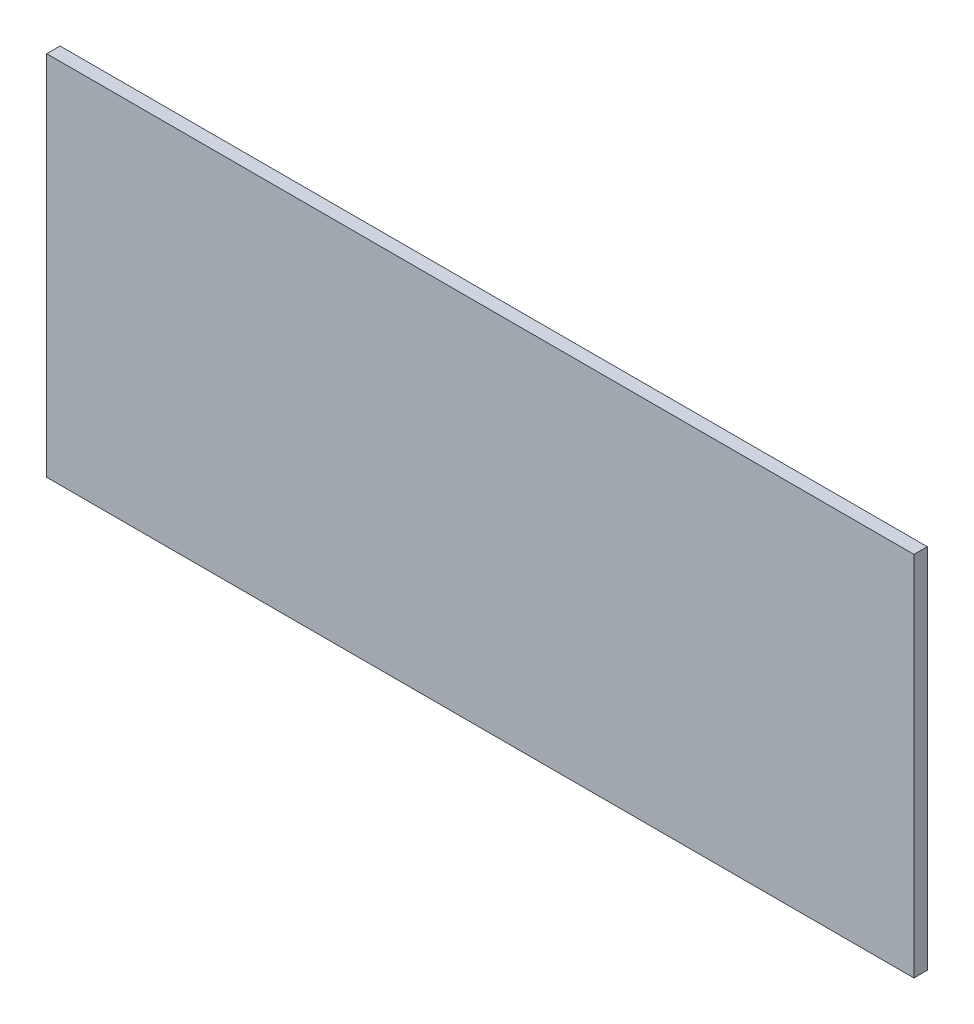
SolidWorks part; units mm, degrees
ref_plane "Plan de face" through (0, 0, 0) normal (0, 0, 1) x (1, 0, 0)
ref_plane "Plan de dessus" through (0, 0, 0) normal (0, 1, 0) x (1, 0, 0)
ref_plane "Plan de droite" through (0, 0, 0) normal (1, 0, 0) x (0, 0, -1)
sketch "Esquisse1" plane through (0, 0, 0) normal (0, 0, 1) x (1, 0, 0)
  line L1 (-65, -27.5) -> (65, -27.5)
  line L2 (-65, -27.5) -> (-65, 27.5)
  line L3 (-65, 27.5) -> (65, 27.5)
  line L4 (65, -27.5) -> (65, 27.5)
  line L5 (-65, -27.5) -> (65, 27.5) construction
  line L6 (-65, 27.5) -> (65, -27.5) construction
  point P0 (0, 0)
  dimension "D1" = 130
  dimension "D2" = 55
extrude "Boss.-Extru.1" add sketch "Esquisse1" along normal blind 2 contours L3 L4 L1 L2
